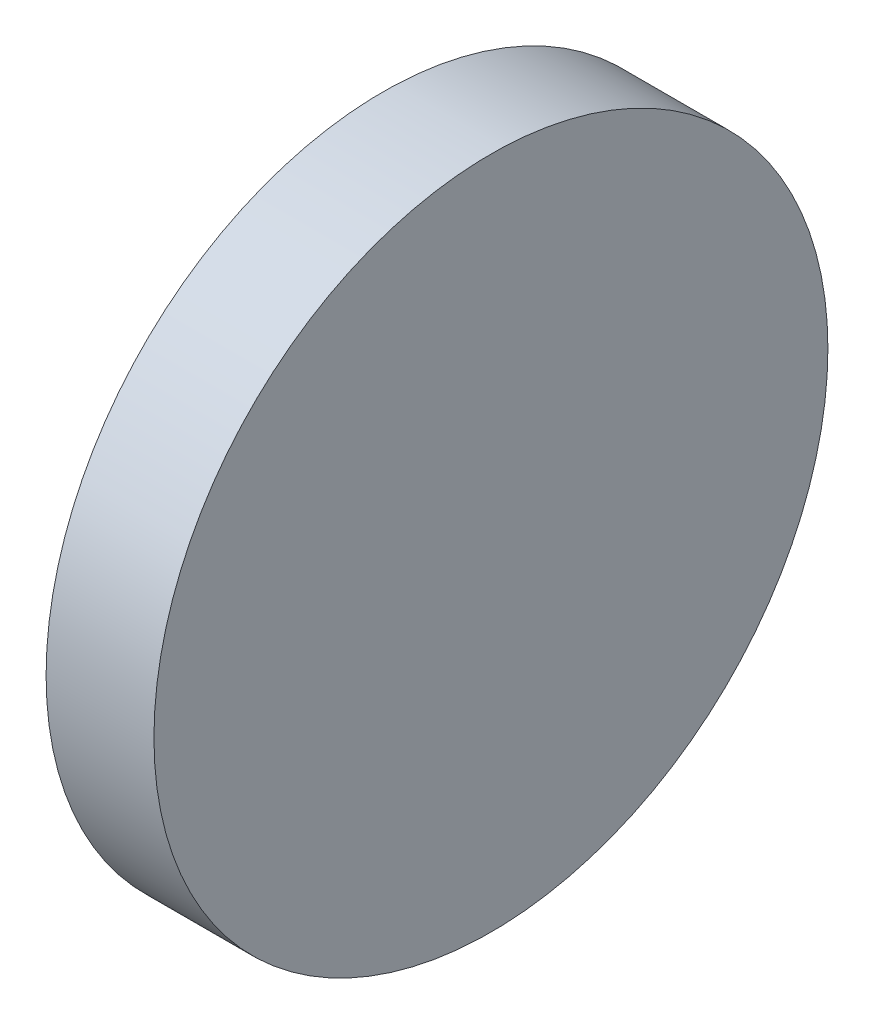
SolidWorks part; units mm, degrees
ref_plane "前视基准面" through (0, 0, 0) normal (0, 0, 1) x (1, 0, 0)
ref_plane "上视基准面" through (0, 0, 0) normal (0, 1, 0) x (1, 0, 0)
ref_plane "右视基准面" through (0, 0, 0) normal (1, 0, 0) x (0, 0, -1)
sketch "草图1" plane through (0, 0, 0) normal (0, 0, 1) x (1, 0, 0)
  line L0 (127.0004, 38.6466) -> (135.3062, 38.6466) construction
  line L1 (130.0786, 38.6466) -> (130.0786, 44.8966)
  line L2 (132.0786, 38.6466) -> (132.0786, 44.8966)
  line L3 (130.0786, 38.6466) -> (132.0786, 38.6466)
  line L5 (130.0786, 44.8966) -> (132.0786, 44.8966)
  dimension "D1" = 6.25
  dimension "D2" = 2
revolve "旋转1" add sketch "草图1" angle 360 about L0
